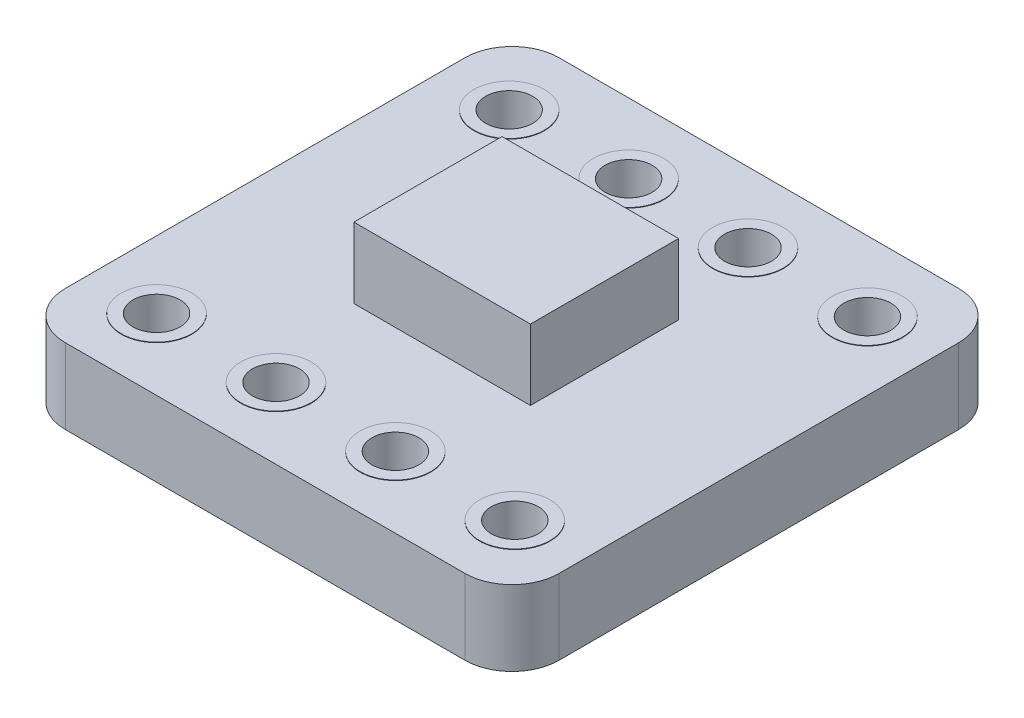
SolidWorks part; units mm, degrees
ref_plane "Front Plane" through (0, 0, 0) normal (0, 0, 1) x (1, 0, 0)
ref_plane "Top Plane" through (0, 0, 0) normal (0, 1, 0) x (1, 0, 0)
ref_plane "Right Plane" through (0, 0, 0) normal (1, 0, 0) x (0, 0, -1)
sketch "Sketch1" plane through (0, 0, 0) normal (0, 1, 0) x (1, 0, 0)
  line L1 (0, 0) -> (10.5, 0)
  line L2 (0, 0) -> (0, 10.5)
  line L3 (0, 10.5) -> (10.5, 10.5)
  line L4 (10.5, 0) -> (10.5, 10.5)
  dimension "D1" = 10.5
  dimension "D2" = 10.5
extrude "Boss-Extrude1" add sketch "Sketch1" along normal blind 1.6
fillet "Fillet1" radius 1 4 edges at (10.5, 0.8, -10.5) (0, 0.8, -10.5) (0, 0.8, 0) (10.5, 0.8, 0)
sketch "Sketch2" plane through (0, 1.6, 0) normal (0, 1, 0) x (1, 0, 0)
  line L0 (10.5, 1) -> (10.5, 9.5) construction
  line L1 (1, 0) -> (9.5, 0) construction
  line L2 (10.5, 5.25) -> (11.9492, 5.25)
  circle A0 centre (1.44, 1.5) radius 0.5
  circle A1 centre (1.44, 1.5) radius 0.75
  circle A2 centre (3.98, 1.5) radius 0.5
  circle A3 centre (3.98, 1.5) radius 0.75
  circle A4 centre (6.52, 1.5) radius 0.5
  circle A5 centre (6.52, 1.5) radius 0.75
  circle A6 centre (9.06, 1.5) radius 0.5
  circle A7 centre (9.06, 1.5) radius 0.75
  circle A8 centre (9.06, 9) radius 0.75
  circle A9 centre (9.06, 9) radius 0.5
  circle A10 centre (6.52, 9) radius 0.75
  circle A11 centre (6.52, 9) radius 0.5
  circle A12 centre (3.98, 9) radius 0.75
  circle A13 centre (3.98, 9) radius 0.5
  circle A14 centre (1.44, 9) radius 0.75
  circle A15 centre (1.44, 9) radius 0.5
  dimension "D1" = 1
  dimension "D2" = 1.5
  dimension "D4" = 1.44
  dimension "D5" = 1.5
  dimension "D3" = 4
extrude "Boss-Extrude2" add sketch "Sketch2" along normal blind 0.01 contours A10 A11 | A12 A13 | A1 A0 | A3 A2 | A15 | A5 A4 | A7 A6 | A8 | A14 | A9
sketch "Sketch4" plane through (0, 1.6, 0) normal (0, 1, 0) x (1, 0, 0)
  circle A1 centre (9.06, 1.5) radius 0.5
  circle A2 centre (9.06, 1.5) radius 0.5
  circle A3 centre (6.52, 1.5) radius 0.5
  circle A4 centre (6.52, 1.5) radius 0.5
  circle A5 centre (3.98, 1.5) radius 0.5
  circle A6 centre (3.98, 1.5) radius 0.5
  circle A7 centre (1.44, 1.5) radius 0.5
  circle A8 centre (1.44, 1.5) radius 0.5
  circle A9 centre (1.44, 9) radius 0.5
  circle A10 centre (1.44, 9) radius 0.5
  circle A11 centre (3.98, 9) radius 0.5
  circle A12 centre (3.98, 9) radius 0.5
  circle A13 centre (6.52, 9) radius 0.5
  circle A14 centre (6.52, 9) radius 0.5
  circle A15 centre (9.06, 9) radius 0.5
  circle A16 centre (9.06, 9) radius 0.5
  dimension "D1" = 0
  dimension "D2" = 0
  dimension "D3" = 0
  dimension "D4" = 0
  dimension "D5" = 0
  dimension "D6" = 0
  dimension "D7" = 0
  dimension "D8" = 0
extrude "Cut-Extrude1" cut sketch "Sketch4" against normal blind 2
sketch "Sketch5" plane through (0, 1.6, 0) normal (0, 1, 0) x (1, 0, 0)
  line L1 (3.3466, 6.9412) -> (7.102, 6.9412)
  line L2 (3.3466, 6.9412) -> (3.3466, 3.7903)
  line L3 (3.3466, 3.7903) -> (7.102, 3.7903)
  line L4 (7.102, 6.9412) -> (7.102, 3.7903)
extrude "Boss-Extrude3" add sketch "Sketch5" along normal blind 1.5 separate body
